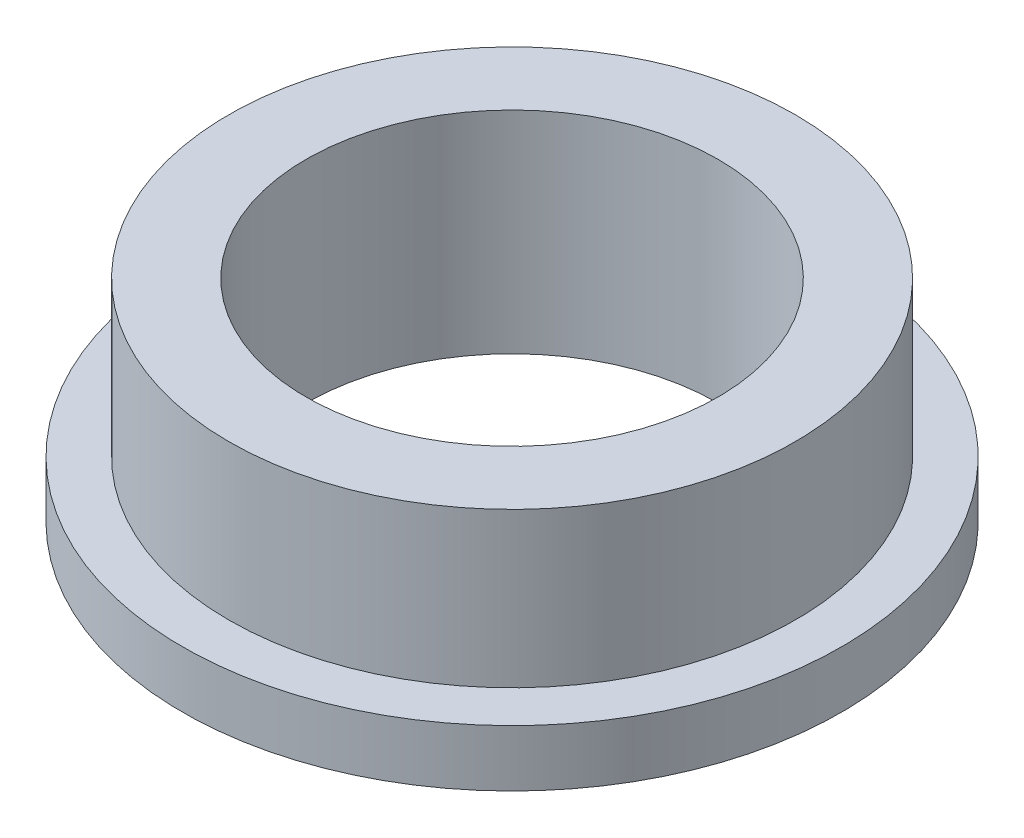
SolidWorks part; units mm, degrees
ref_plane "Front Plane" through (0, 0, 0) normal (0, 0, 1) x (1, 0, 0)
ref_plane "Top Plane" through (0, 0, 0) normal (0, 1, 0) x (1, 0, 0)
ref_plane "Right Plane" through (0, 0, 0) normal (1, 0, 0) x (0, 0, -1)
sketch "Sketch1" plane through (0, 0, 0) normal (0, 0, 1) x (1, 0, 0)
  line L0 (0, 0) -> (0, 6.2518) construction
  line L1 (-6.4, 0) -> (-4, 0)
  line L2 (-4, 0) -> (-4, 4.1)
  line L3 (-4, 4.1) -> (-5.5, 4.1)
  line L4 (-5.5, 4.1) -> (-5.5, 1.1)
  line L5 (-5.5, 1.1) -> (-6.4, 1.1)
  line L6 (-6.4, 1.1) -> (-6.4, 0)
  dimension "D1" = 1.1
  dimension "D2" = 6.4
  dimension "D3" = 5.5
  dimension "D4" = 4
  dimension "D5" = 4.1
revolve "Revolve1" add sketch "Sketch1" angle 360 about L0
